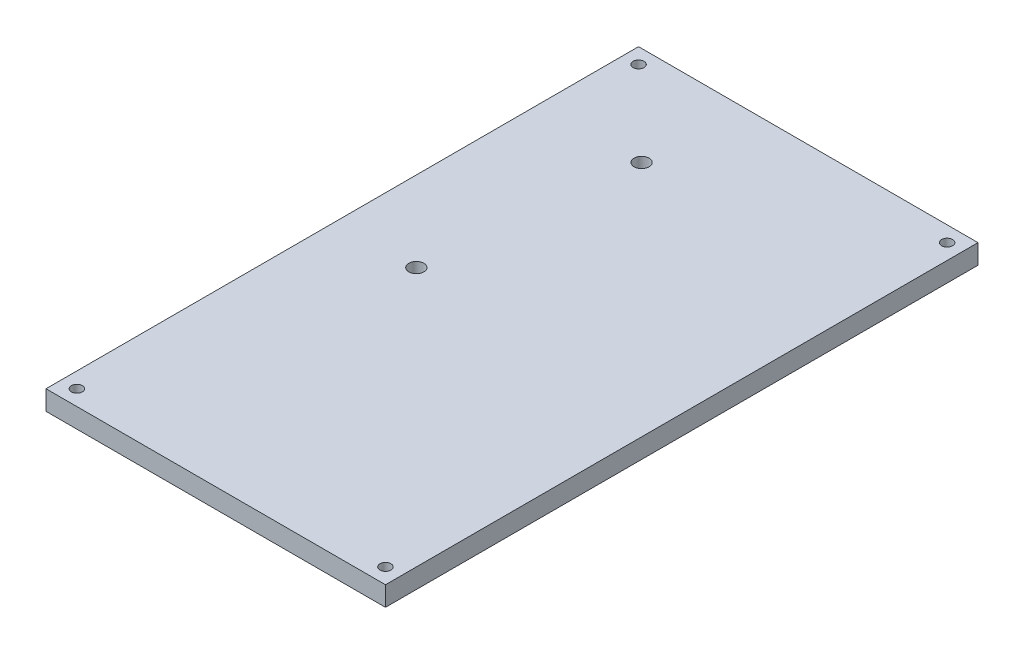
SolidWorks part; units mm, degrees
material "FRP Fiberglass"
ref_plane "Front Plane" through (0, 0, 0) normal (0, 0, 1) x (1, 0, 0)
ref_plane "Top Plane" through (0, 0, 0) normal (0, 1, 0) x (1, 0, 0)
ref_plane "Right Plane" through (0, 0, 0) normal (1, 0, 0) x (0, 0, -1)
sketch "Sketch2" plane through (0, 0, 0) normal (0, 1, 0) x (1, 0, 0)
  line L1 (0, 0) -> (55, 0)
  line L2 (0, 0) -> (0, 96)
  line L3 (0, 96) -> (55, 96)
  line L4 (55, 0) -> (55, 96)
  dimension "D1" = 96
  dimension "D2" = 55
extrude "Boss-Extrude1" add sketch "Sketch2" along normal blind 3.175
sketch "Sketch3" plane through (0, 3.175, 0) normal (0, 1, 0) x (1, 0, 0)
  line L0 (2.5, 2.5) -> (52.5, 2.5) construction
  line L1 (52.5, 2.5) -> (52.5, 93.5) construction
  line L2 (0, 0) -> (55, 0) construction
  line L3 (55, 0) -> (55, 96) construction
  line L4 (0, 96) -> (0, 0) construction
  line L5 (55, 96) -> (0, 96) construction
  line L6 (2.5, 93.5) -> (52.5, 93.5) construction
  line L9 (2.5, 93.5) -> (2.5, 2.5) construction
  circle A0 centre (2.5, 2.5) radius 0.762
  circle A1 centre (52.5, 2.5) radius 0.762
  circle A2 centre (52.5, 93.5) radius 0.762
  circle A3 centre (2.5, 93.5) radius 0.762
  dimension "D1" = 1.524
  dimension "D2" = 2.5
  dimension "D3" = 2.5
  dimension "D4" = 2.5
  dimension "D5" = 2.5
sketch "Sketch4" plane through (0, 3.175, 0) normal (0, 1, 0) x (1, 0, 0)
  line L0 (55, 96) -> (0, 96) construction
  line L1 (16.5, 80) -> (13, 80) construction
  line L3 (0, 0) -> (55, 0) construction
  line L7 (0, 96) -> (0, 0) construction
  line L10 (55, 0) -> (55, 96) construction
  line L19 (55, 48) -> (0, 48) construction
  line L20 (5, 91) -> (5, 96) construction
  line L21 (5, 91) -> (0, 91) construction
  line L22 (50, 91) -> (50, 85) construction
  line L23 (21, 85) -> (50, 85) construction
  line L24 (21, 12) -> (21, 85) construction
  line L25 (5, 12) -> (21, 12) construction
  line L26 (5, 91) -> (5, 0) construction
  line L27 (13, 12) -> (13, 96) construction
  line L28 (50, 91) -> (5, 91) construction
  line L29 (5, 95) -> (50, 95) construction
  line L30 (50, 91) -> (50, 96) construction
  line L31 (50, 91) -> (55, 91) construction
  point P23 (16.5, 80)
  point P27 (13, 47)
  dimension "D1" = 16
  dimension "D2" = 45
  dimension "D3" = 83
  dimension "D4" = 10
  dimension "D5" = 35
  dimension "D6" = 5
  dimension "D7" = 1
  dimension "D8" = 3.5
hole_wizard "#2 Clearance Hole1" positions "Sketch8" profile "Sketch9" hole size "#2" standard "ANSI Inch" end condition through all
sketch "Sketch8" plane through (0, 3.175, 0) normal (0, 1, 0) x (1, 0, 0)
  point P0 (16.5, 80)
  point P3 (13, 47)
sketch "Sketch9" plane through (16.5, 3.175, -80) normal (1, 0, 0) x (0, 0, 1)
  line L0 (0, 0) -> (0, 3.175)
  line L1 (0, 3.175) -> (1.2192, 3.175)
  line L2 (1.2192, 3.175) -> (1.2192, 0)
  line L5 (1.2192, 0) -> (0, 0)
  line L11 (0, -6.35) -> (0, 107.95) construction
  dimension "Thru Hole Dia." = 2.4384
  dimension "Thru Hole Depth" = 3.175
hole_wizard "#0 Clearance Hole1" positions "Sketch10" profile "Sketch11" hole size "#0" standard "ANSI Inch" end condition through all
sketch "Sketch10" plane through (0, 3.175, 0) normal (0, 1, 0) x (1, 0, 0)
  point P0 (2.5, 2.5)
  point P3 (52.5, 2.5)
  point P6 (52.5, 93.5)
  point P9 (2.5, 93.5)
sketch "Sketch11" plane through (2.5, 3.175, -2.5) normal (1, 0, 0) x (0, 0, 1)
  line L0 (0, 0) -> (0, 3.175)
  line L1 (0, 3.175) -> (0.889, 3.175)
  line L2 (0.889, 3.175) -> (0.889, 0)
  line L5 (0.889, 0) -> (0, 0)
  line L11 (0, -6.35) -> (0, 107.95) construction
  dimension "Thru Hole Dia." = 1.778
  dimension "Thru Hole Depth" = 3.175
hole_wizard "#0 Clearance Hole3" positions "Sketch18" profile "Sketch19" hole size "#0" standard "ANSI Inch"
sketch "Sketch18" plane through (0, 0, 0) normal (0, -1, 0) x (-1, 0, 0)
  point P0 (-43.2, 15.3502)
  point P3 (-25.2, 15.3502)
sketch "Sketch19" plane through (43.2, 0, -15.3502) normal (1, 0, 0) x (0, 0, -1)
  line L0 (0, 0) -> (0, 3.5342)
  line L1 (0, 3.5342) -> (0.889, 3)
  line L2 (0.889, 3) -> (0.889, 0)
  line L5 (0.889, 0) -> (0, 0)
  line L10 (0, 3.5342) -> (-0.889, 3) construction
  line L11 (0, -6.35) -> (0, 107.95) construction
  dimension "Hole Dia." = 1.778
  dimension "Hole Depth" = 3
  dimension "Drill Angle" = 118
